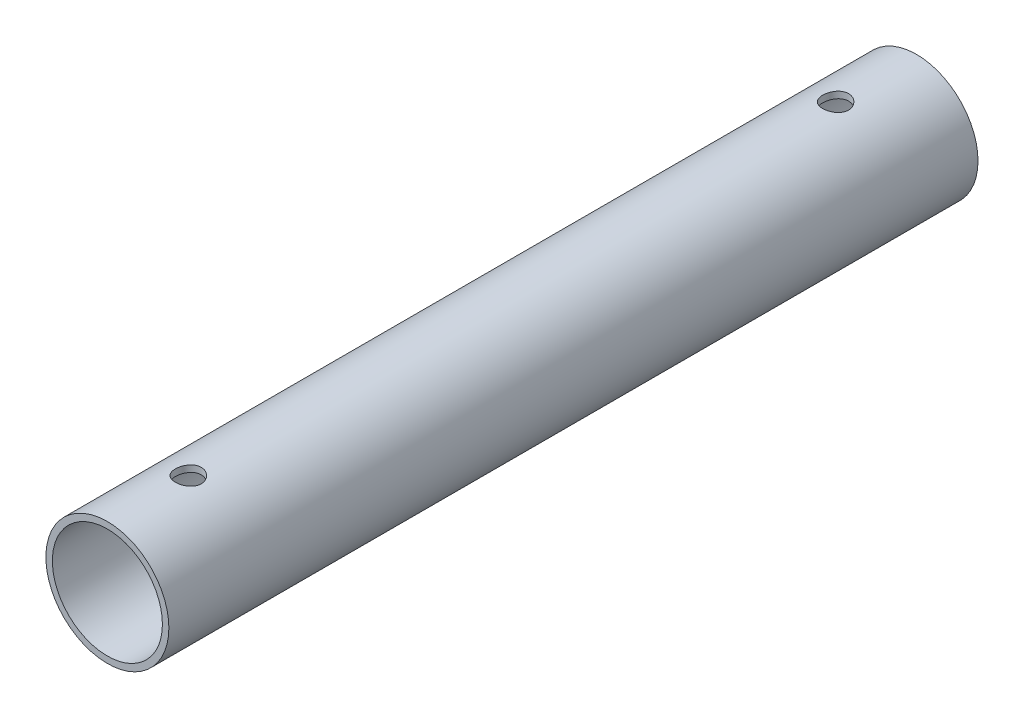
SolidWorks part; units mm, degrees
ref_plane "Front Plane" through (0, 0, 0) normal (0, 0, 1) x (1, 0, 0)
ref_plane "Top Plane" through (0, 0, 0) normal (0, 1, 0) x (1, 0, 0)
ref_plane "Right Plane" through (0, 0, 0) normal (1, 0, 0) x (0, 0, -1)
sketch "Sketch1" plane through (0, 0, 0) normal (0, 0, 1) x (1, 0, 0)
  circle A0 centre (0, 0) radius 17
  circle A1 centre (0, 0) radius 19
  dimension "D1" = 34
  dimension "D2" = 2
extrude "Boss-Extrude1" add sketch "Sketch1" along normal mid plane 250
ref_plane "Plane1" through (0, 18, 0) normal (0, 1, 0) x (1, 0, 0)
ref_plane "Plane2" through (0, 21, 0) normal (0, 1, 0) x (1, 0, 0)
sketch "Sketch4" plane through (0, 21, 0) normal (0, 1, 0) x (1, 0, 0)
  line L0 (0, 25.0813) -> (0, -59.2901) construction
  line L1 (-19, -125) -> (19, -125) construction
  circle A0 centre (0, -100) radius 4
  dimension "D1" = 8
  dimension "D2" = 25
extrude "Cut-Extrude3" cut sketch "Sketch4" against normal through all
mirror "Mirror1" about plane through (0, 0, 0) normal (0, 0, 1) of "Cut-Extrude3"
